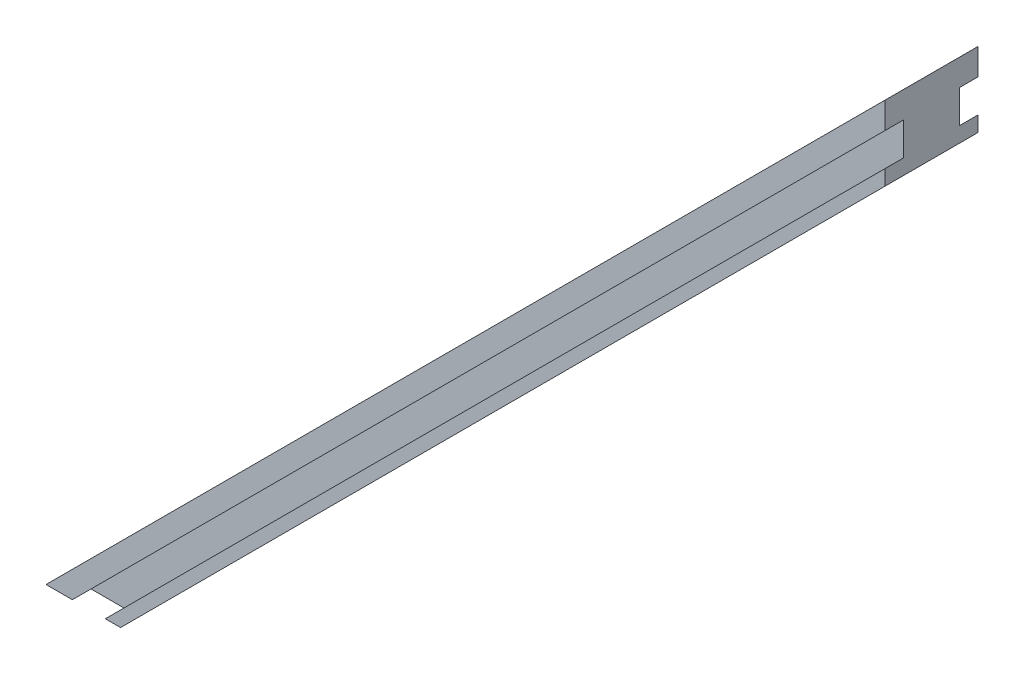
SolidWorks part; units mm, degrees
ref_plane "Front Plane" through (0, 0, 0) normal (0, 0, 1) x (1, 0, 0)
ref_plane "Top Plane" through (0, 0, 0) normal (0, 1, 0) x (1, 0, 0)
ref_plane "Right Plane" through (0, 0, 0) normal (1, 0, 0) x (0, 0, -1)
sketch "Sketch1" plane through (0, 0, 0) normal (0, 0, 1) x (1, 0, 0)
  line L0 (-45, -45) -> (45, 45)
  line L1 (45, 45) -> (45, 37)
  line L2 (-37, -45) -> (45, 37)
  line L6 (-45, -45) -> (-37, -45)
  point P4 (7.5, -7.5)
  point P13 (0, 0)
  dimension "D1" = 45
  dimension "D2" = 8
  dimension "D3" = 90
  dimension "D5" = 127.2792
extrude "Main" add sketch "Sketch1" along normal mid plane 10
sketch "Sketch4" plane through (0, 0, 5) normal (0, 0, 1) x (1, 0, 0)
  line L0 (45, 42.1716) -> (-42.1716, -45)
  line L1 (-42.1716, -45) -> (-38.636, -45)
  line L2 (-38.636, -45) -> (45, 38.636)
  line L3 (45, 38.636) -> (45, 42.1716)
  line L4 (45, 45) -> (-45, -45) construction
  line L5 (-45, -45) -> (-37, -45) construction
  line L6 (45, 37) -> (45, 45) construction
  dimension "D1" = 2.5
  dimension "D2" = 2
  dimension "D3" = 123.2792
  dimension "D4" = 118.2792
extrude "WindowSlot1" cut sketch "Sketch4" against normal blind 2
mirror "Mirror1" about plane through (0, 0, 0) normal (0, 0, 1) of "WindowSlot1"
sketch "Sketch6" plane through (4, -4, 0) normal (-0.7071, 0.7071, 0) x (0, 0, 1)
  circle A0 centre (0, 50) radius 1.25
  dimension "D1" = 2.5
  dimension "D2" = 50
extrude "Cut-Extrude2" cut sketch "Sketch6" along normal blind 5
pattern_linear "LPattern1" count 11 spacing 10 along (-0.7071, -0.7071, 0) of "Cut-Extrude2"
sketch "Sketch7" plane through (0, 0, 0) normal (-0.7071, 0.7071, 0) x (0, 0, 1)
  circle A0 centre (0, 40) radius 3.5
  circle A2 centre (0, -40) radius 3.5
  circle A3 centre (0, 40) radius 1.25 construction
  dimension "D1" = 7
  dimension "D2" = 80
extrude "Cut-Extrude4" cut sketch "Sketch7" against normal blind 1.5
